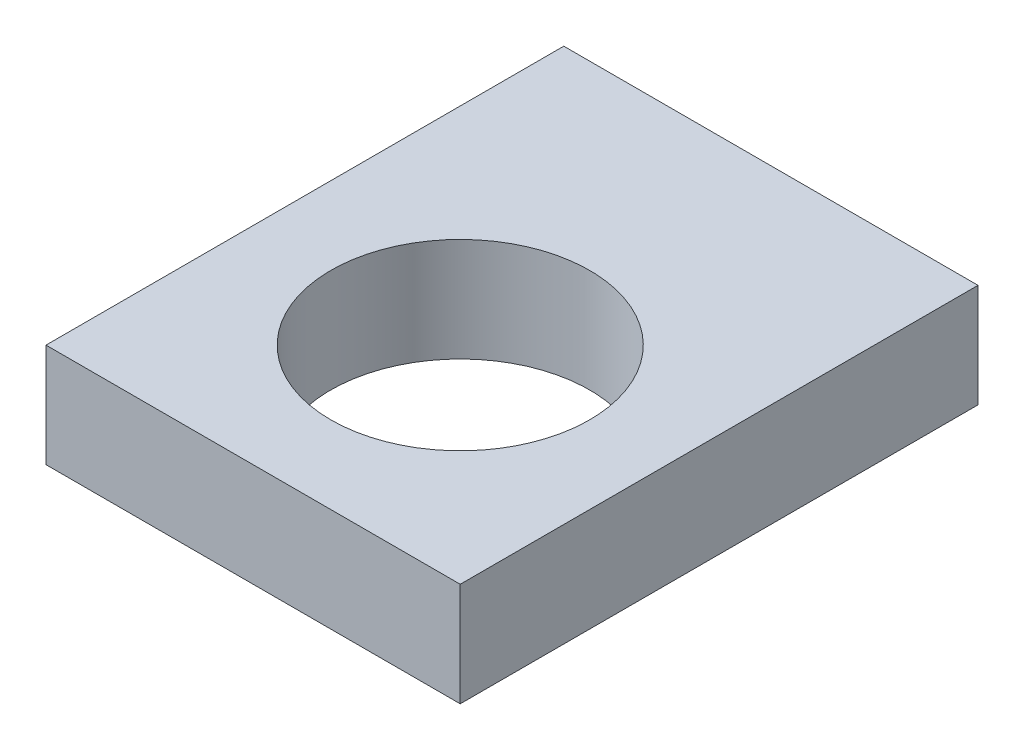
SolidWorks part; units mm, degrees
material "1060 Alloy"
ref_plane "Front Plane" through (0, 0, 0) normal (0, 0, 1) x (1, 0, 0)
ref_plane "Top Plane" through (0, 0, 0) normal (0, 1, 0) x (1, 0, 0)
ref_plane "Right Plane" through (0, 0, 0) normal (1, 0, 0) x (0, 0, -1)
sketch "Sketch1" plane through (0, 0, 0) normal (0, 1, 0) x (1, 0, 0)
  line L1 (25.4, 38.1) -> (-25.4, 38.1)
  line L2 (25.4, 38.1) -> (25.4, -25.4)
  line L3 (25.4, -25.4) -> (-25.4, -25.4)
  line L4 (-25.4, 38.1) -> (-25.4, -25.4)
  line L5 (25.4, 38.1) -> (-25.4, -25.4) construction
  line L6 (25.4, -25.4) -> (-25.4, 38.1) construction
  line L7 (0, -6.985) -> (0, 6.985) construction
  point P0 (0, 6.35)
  dimension "D1" = 50.8
  dimension "D2" = 63.5
  dimension "D3" = 25.4
extrude "Boss-Extrude1" add sketch "Sketch1" along normal mid plane 12.7
sketch "Sketch2" plane through (0, 6.35, 0) normal (0, 1, 0) x (1, 0, 0)
  circle A0 centre (0, 0) radius 15.875
  dimension "D1" = 31.75
extrude "Cut-Extrude1" cut sketch "Sketch2" against normal through all
sketch "Sketch3" plane through (0, 0, -38.1) normal (0, 0, -1) x (-1, 0, 0)
  line L0 (15.875, 0) -> (-15.875, 0) construction
  line L1 (0, 6.985) -> (0, -6.985) construction
  line L2 (27.94, 0) -> (-27.94, 0) construction
  circle A0 centre (-15.875, 0) radius 3.175
  circle A1 centre (15.875, 0) radius 3.175
  point P2 (0, 0)
  dimension "D1" = 6.35
  dimension "D2" = 31.75
extrude "Cut-Extrude2" cut sketch "Sketch3" against normal blind 12.7
